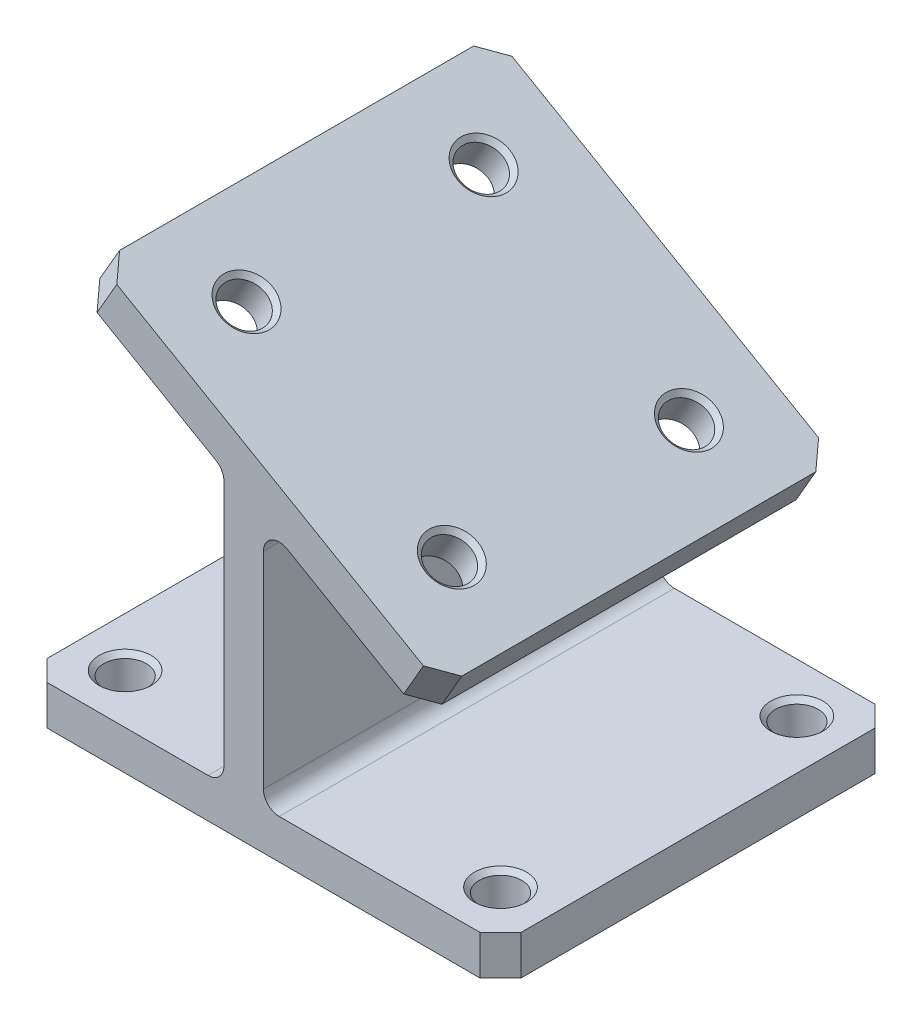
SolidWorks part; units mm, degrees
material "1060 Alloy"
ref_plane "Front Plane" through (0, 0, 0) normal (0, 0, 1) x (1, 0, 0)
ref_plane "Top Plane" through (0, 0, 0) normal (0, 1, 0) x (1, 0, 0)
ref_plane "Right Plane" through (0, 0, 0) normal (1, 0, 0) x (0, 0, -1)
sketch "Sketch1" plane through (0, 0, 0) normal (0, 0, 1) x (1, 0, 0)
  line L0 (0, 2.54) -> (0, 42.2644)
  line L1 (-1.27, 44.4641) -> (-23.2426, 57.15)
  line L2 (-23.2426, 57.15) -> (-20.0676, 62.6493)
  line L3 (-20.0676, 62.6493) -> (34.925, 30.8993)
  line L4 (34.925, 30.8993) -> (31.75, 25.4)
  line L5 (31.75, 25.4) -> (10.16, 37.865)
  line L6 (6.35, 35.6653) -> (6.35, 2.54)
  line L7 (8.89, 0) -> (44.45, 0)
  line L8 (44.45, 0) -> (44.45, -6.35)
  line L9 (44.45, -6.35) -> (-31.75, -6.35)
  line L10 (-31.75, -6.35) -> (-31.75, 0)
  line L11 (-31.75, 0) -> (-2.54, 0)
  arc A0 (6.35, 2.54) -> (8.89, 0) centre (8.89, 2.54) ccw
  arc A1 (0, 2.54) -> (-2.54, 0) centre (-2.54, 2.54) cw
  arc A2 (10.16, 37.865) -> (6.35, 35.6653) centre (8.89, 35.6653) ccw
  arc A3 (0, 42.2644) -> (-1.27, 44.4641) centre (-2.54, 42.2644) ccw
  point P4 (0, 0)
  point P18 (0, 0)
  dimension "D10" = 2.54
  dimension "D1" = 76.2
  dimension "D2" = 31.75
  dimension "D3" = 6.35
  dimension "D4" = 6.35
  dimension "D5" = 31.75
  dimension "D6" = 30
  dimension "D7" = 6.35
  dimension "D8" = 63.5
  dimension "D9" = 63.5
extrude "Boss-Extrude1" add sketch "Sketch1" along normal mid plane 63.5
chamfer "Chamfer1" distance 3.302 angle 45 8 edges at (-31.75, -3.175, 31.75) (-31.75, -3.175, -31.75) (44.45, -3.175, -31.75) (44.45, -3.175, 31.75) (33.3375, 28.1496, -31.75) (-21.6551, 59.8996, -31.75) (-21.6551, 59.8996, 31.75) (33.3375, 28.1496, 31.75)
sketch "Sketch2" plane through (22.111, 38.2974, 0) normal (0.5, 0.866, 0) x (0.866, -0.5, 0)
  line L0 (-48.7037, -28.448) -> (-48.7037, 28.448) construction
  line L1 (-36.0037, 19.05) -> (2.0963, 19.05) construction
  line L2 (-36.0037, 19.05) -> (-36.0037, -19.05) construction
  line L3 (-36.0037, -19.05) -> (2.0963, -19.05) construction
  line L4 (2.0963, 19.05) -> (2.0963, -19.05) construction
  line L5 (-36.0037, 19.05) -> (2.0963, -19.05) construction
  line L6 (-36.0037, -19.05) -> (2.0963, 19.05) construction
  line L7 (11.4943, -31.75) -> (-45.4017, -31.75) construction
  circle A0 centre (-36.0037, 19.05) radius 3.429
  circle A1 centre (2.0963, 19.05) radius 3.429
  circle A2 centre (-36.0037, -19.05) radius 3.429
  circle A3 centre (2.0963, -19.05) radius 3.429
  point P0 (-16.9537, 0)
  dimension "D5" = 6.858
  dimension "D1" = 38.1
  dimension "D2" = 38.1
  dimension "D3" = 31.75
  dimension "D4" = 31.75
extrude "Cut-Extrude1" cut sketch "Sketch2" against normal up to next
sketch "Sketch3" plane through (0, -6.35, 0) normal (0, -1, 0) x (1, 0, 0)
  line L1 (-23.8125, 23.8125) -> (36.5125, 23.8125) construction
  line L2 (-23.8125, 23.8125) -> (-23.8125, -23.8125) construction
  line L3 (-23.8125, -23.8125) -> (36.5125, -23.8125) construction
  line L4 (36.5125, 23.8125) -> (36.5125, -23.8125) construction
  line L5 (-23.8125, 23.8125) -> (36.5125, -23.8125) construction
  line L6 (-23.8125, -23.8125) -> (36.5125, 23.8125) construction
  line L7 (44.45, 28.448) -> (44.45, -28.448) construction
  circle A0 centre (-23.8125, 23.8125) radius 3.429
  circle A1 centre (36.5125, 23.8125) radius 3.429
  circle A2 centre (-23.8125, -23.8125) radius 3.429
  circle A3 centre (36.5125, -23.8125) radius 3.429
  point P0 (6.35, 0)
  point P7 (44.45, 0)
  dimension "D3" = 6.858
  dimension "D1" = 47.625
  dimension "D2" = 60.325
extrude "Cut-Extrude2" cut sketch "Sketch3" against normal up to next
chamfer "Chamfer2" distance 0.762 angle 45 16 edges at (-23.8125, 0, -27.2415) (-20.3835, -6.35, -23.8125) (-23.8125, 0, 20.3835) (-20.3835, -6.35, 23.8125) (39.9415, 0, -23.8125) (39.9415, -6.35, -23.8125) (39.9415, 0, 23.8125) (39.9415, -6.35, 23.8125) (17.7819, 33.4645, -19.05) (20.9569, 38.9638, -19.05) (17.7819, 33.4645, 19.05) (20.9569, 38.9638, 19.05) (-15.2137, 52.5145, -19.05) (-12.0387, 58.0138, -19.05) (-15.2137, 52.5145, 19.05) (-12.0387, 58.0138, 19.05)
